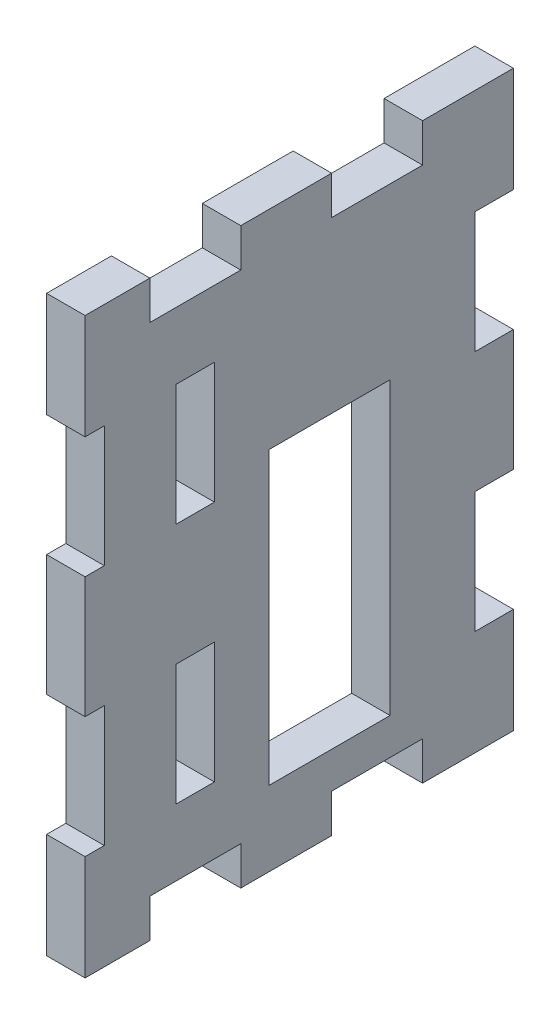
SolidWorks part; units mm, degrees
ref_plane "Front Plane" through (0, 0, 0) normal (0, 0, 1) x (1, 0, 0)
ref_plane "Top Plane" through (0, 0, 0) normal (0, 1, 0) x (1, 0, 0)
ref_plane "Right Plane" through (0, 0, 0) normal (1, 0, 0) x (0, 0, -1)
sketch "Sketch1" plane through (0, 0, 0) normal (1, 0, 0) x (0, 0, -1)
  line L1 (0, 0) -> (35.35, 0)
  line L2 (0, 0) -> (0, 47.35)
  line L3 (0, 47.35) -> (35.35, 47.35)
  line L4 (35.35, 0) -> (35.35, 47.35)
  line L5 (25.175, 6.175) -> (15.175, 6.175)
  line L6 (25.175, 6.175) -> (25.175, 30.175)
  line L7 (25.175, 30.175) -> (15.175, 30.175)
  line L8 (15.175, 6.175) -> (15.175, 30.175)
  dimension "D1" = 47.35
  dimension "D2" = 35.35
  dimension "D3" = 10.175
  dimension "D4" = 6.175
  dimension "D5" = 24
  dimension "D6" = 10
extrude "Boss-Extrude1" add sketch "Sketch1" along normal blind 3.175
sketch "Sketch2" plane through (3.175, 0, 0) normal (1, 0, 0) x (0, 0, -1)
  line L0 (35.35, 0) -> (35.35, 47.35) construction
  line L1 (35.35, 38.675) -> (32.175, 38.675)
  line L2 (35.35, 38.675) -> (35.35, 28.675)
  line L3 (35.35, 28.675) -> (32.175, 28.675)
  line L4 (32.175, 38.675) -> (32.175, 28.675)
  line L5 (0, 47.35) -> (0, 0) construction
  line L6 (35.35, 18.675) -> (32.175, 18.675)
  line L7 (35.35, 18.675) -> (35.35, 8.675)
  line L8 (35.35, 8.675) -> (32.175, 8.675)
  line L9 (32.175, 18.675) -> (32.175, 8.675)
  line L10 (10.675, 8.675) -> (7.5, 8.675)
  line L11 (10.675, 8.675) -> (10.675, 18.675)
  line L12 (10.675, 18.675) -> (7.5, 18.675)
  line L13 (7.5, 8.675) -> (7.5, 18.675)
  line L14 (10.675, 28.675) -> (7.5, 28.675)
  line L15 (10.675, 28.675) -> (10.675, 38.675)
  line L16 (10.675, 38.675) -> (7.5, 38.675)
  line L17 (7.5, 28.675) -> (7.5, 38.675)
  line L18 (0, 38.675) -> (1.5875, 38.675)
  line L19 (0, 38.675) -> (0, 28.675)
  line L20 (0, 28.675) -> (1.5875, 28.675)
  line L21 (1.5875, 38.675) -> (1.5875, 28.675)
  line L22 (35.35, 47.35) -> (0, 47.35) construction
  line L23 (0, 18.675) -> (1.5875, 18.675)
  line L24 (0, 18.675) -> (0, 8.675)
  line L25 (0, 8.675) -> (1.5875, 8.675)
  line L26 (1.5875, 18.675) -> (1.5875, 8.675)
  line L27 (27.85, 47.35) -> (20.35, 47.35)
  line L28 (27.85, 47.35) -> (27.85, 44.175)
  line L29 (27.85, 44.175) -> (20.35, 44.175)
  line L30 (20.35, 47.35) -> (20.35, 44.175)
  line L31 (0, 0) -> (35.35, 0) construction
  line L32 (5.35, 47.35) -> (12.85, 47.35)
  line L33 (5.35, 47.35) -> (5.35, 44.175)
  line L34 (5.35, 44.175) -> (12.85, 44.175)
  line L35 (12.85, 47.35) -> (12.85, 44.175)
  line L36 (5.35, 0) -> (12.85, 0)
  line L37 (5.35, 0) -> (5.35, 3.175)
  line L38 (5.35, 3.175) -> (12.85, 3.175)
  line L39 (12.85, 0) -> (12.85, 3.175)
  line L41 (27.85, 3.175) -> (20.35, 3.175)
  line L42 (27.85, 3.175) -> (27.85, 0)
  line L43 (27.85, 0) -> (20.35, 0)
  line L44 (20.35, 3.175) -> (20.35, 0)
  point P28 (0, 23.675)
  dimension "D1" = 10
  dimension "D2" = 10
  dimension "D3" = 5
  dimension "D4" = 1.5875
  dimension "D5" = 3.175
  dimension "D6" = 5.9125
  dimension "D7" = 3.175
  dimension "D8" = 7.5
  dimension "D9" = 7.5
  dimension "D10" = 7.5
  dimension "D11" = 3.175
extrude "Cut-Extrude1" cut sketch "Sketch2" against normal through all
